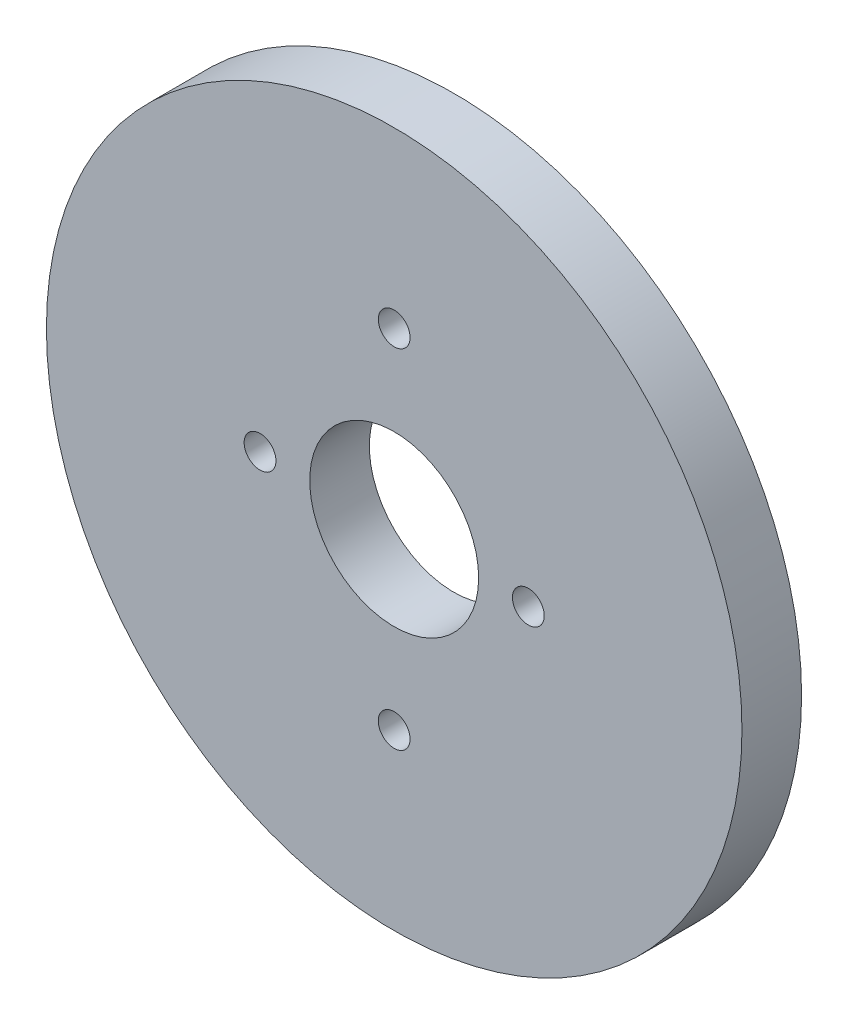
SolidWorks part; units mm, degrees
ref_plane "Front Plane" through (0, 0, 0) normal (0, 0, 1) x (1, 0, 0)
ref_plane "Top Plane" through (0, 0, 0) normal (0, 1, 0) x (1, 0, 0)
ref_plane "Right Plane" through (0, 0, 0) normal (1, 0, 0) x (0, 0, -1)
sketch "Sketch1" plane through (0, 0, 0) normal (0, 0, 1) x (1, 0, 0)
  line L0 (6.75, 0) -> (0, 0) construction
  line L1 (0, 0) -> (0, 8.75) construction
  circle A0 centre (0, 0) radius 4.25
  circle A1 centre (0, 0) radius 17.5
  circle A2 centre (6.75, 0) radius 0.8
  circle A3 centre (0, 8.75) radius 0.8
  circle A4 centre (0, -8.75) radius 0.8
  circle A5 centre (-6.75, 0) radius 0.8
  dimension "D1" = 8.5
  dimension "D2" = 35
  dimension "D4" = 1.6
  dimension "D3" = 6.75
  dimension "D5" = 8.75
extrude "Boss-Extrude1" add sketch "Sketch1" along normal blind 3
